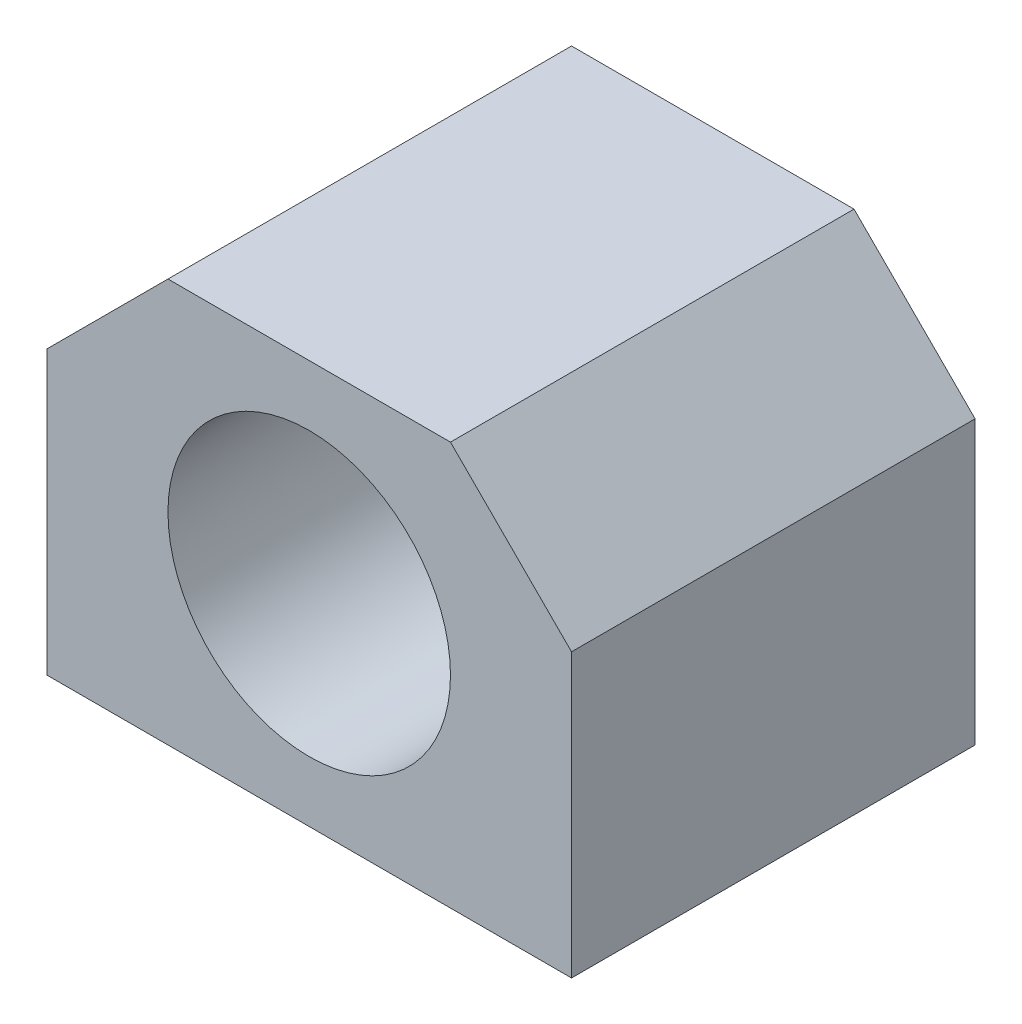
SolidWorks part; units mm, degrees
ref_plane "Front Plane" through (0, 0, 0) normal (0, 0, 1) x (1, 0, 0)
ref_plane "Top Plane" through (0, 0, 0) normal (0, 1, 0) x (1, 0, 0)
ref_plane "Right Plane" through (0, 0, 0) normal (1, 0, 0) x (0, 0, -1)
sketch "Sketch1" plane through (0, 0, 0) normal (0, 0, 1) x (1, 0, 0)
  line L0 (-14, 20) -> (14, 20)
  line L1 (-26, -20) -> (-26, 8)
  line L2 (-26, 8) -> (-14, 20)
  line L3 (-26, -20) -> (26, -20)
  line L4 (0, 20) -> (0, -17.0576) construction
  line L5 (26, -20) -> (26, 8)
  line L6 (26, 8) -> (14, 20)
  line L7 (-26, 8) -> (-26, 20) construction
  line L8 (-26, 20) -> (-14, 20) construction
  line L9 (14, 20) -> (26, 20) construction
  line L10 (26, 20) -> (26, 8) construction
  circle A0 centre (0, 0) radius 14
  dimension "D1" = 28
  dimension "D2" = 52
  dimension "D3" = 20
  dimension "D4" = 40
  dimension "D5" = 45
  dimension "D6" = 12
extrude "Boss-Extrude1" add sketch "Sketch1" along normal blind 40
sketch "Sketch2" plane through (0, -20, 0) normal (0, -1, 0) x (1, 0, 0)
  line L0 (-26, 40) -> (26, 0) construction
  line L2 (20, 8) -> (-20, 8) construction
  line L3 (20, 8) -> (20, 32) construction
  line L4 (20, 32) -> (-20, 32) construction
  line L5 (-20, 8) -> (-20, 32) construction
  line L6 (20, 8) -> (-20, 32) construction
  line L7 (20, 32) -> (-20, 8) construction
  circle A0 centre (-20, 32) radius 2.1
  circle A1 centre (20, 32) radius 2.1
  circle A2 centre (20, 8) radius 2.1
  circle A3 centre (-20, 8) radius 2.1
  point P4 (0, 20)
  dimension "D3" = 4.2
  dimension "D1" = 24
  dimension "D2" = 40
extrude "Cut-Extrude1" cut sketch "Sketch2" against normal blind 10
